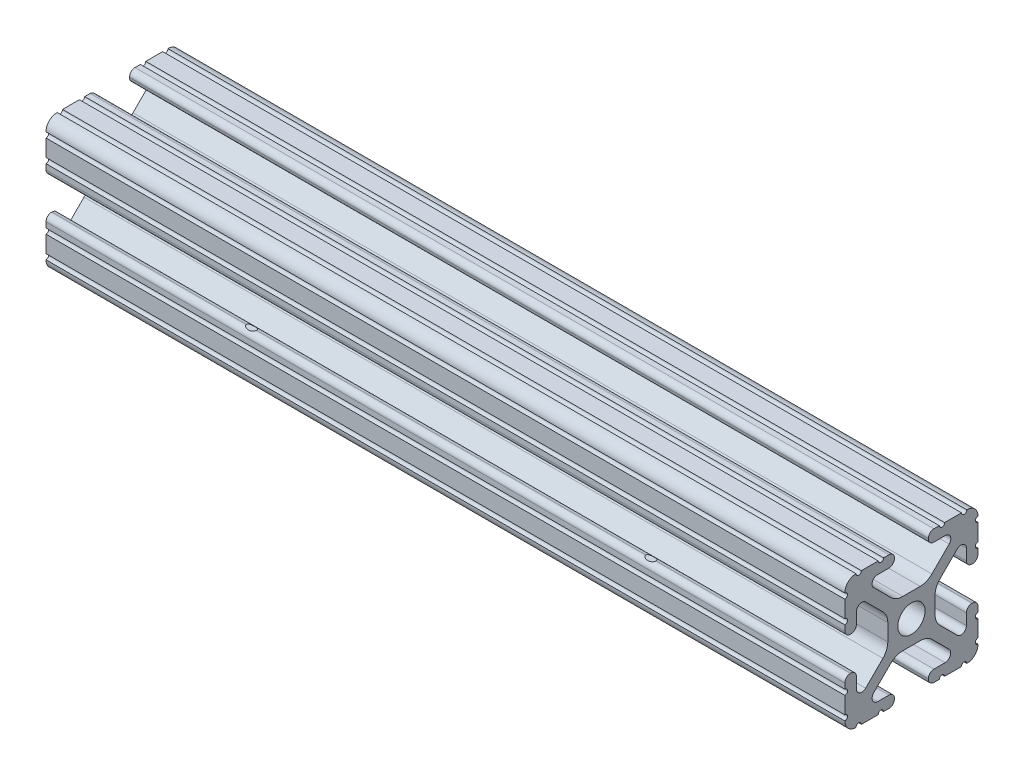
SolidWorks part; units mm, degrees
material "6061-T6 (SS)"
ref_plane "Front Plane" through (0, 0, 0) normal (0, 0, 1) x (1, 0, 0)
ref_plane "Top Plane" through (0, 0, 0) normal (0, 1, 0) x (1, 0, 0)
ref_plane "Right Plane" through (0, 0, 0) normal (1, 0, 0) x (0, 0, -1)
sketch "Sketch1" plane through (0, 0, 0) normal (1, 0, 0) x (0, 0, -1)
  line L0 (6.3331, -12.7) -> (9.5504, -12.7)
  line L1 (12.7, -9.5504) -> (12.7, -6.3331)
  line L2 (12.7, -5.3171) -> (12.7, -4.2875)
  line L3 (11.651, -3.2385) -> (11.5392, -3.2385)
  line L4 (10.4902, -4.2875) -> (10.4902, -6.4021)
  line L5 (8.7371, -7.1294) -> (5.441, -3.8408)
  line L6 (4.5085, -1.5932) -> (4.5085, 1.5932)
  line L7 (5.441, 3.8408) -> (8.7371, 7.1294)
  line L8 (10.4902, 6.4021) -> (10.4902, 4.2875)
  line L9 (11.5392, 3.2385) -> (11.651, 3.2385)
  line L10 (12.7, 4.2875) -> (12.7, 5.3171)
  line L11 (12.7, 6.3331) -> (12.7, 9.5504)
  line L12 (9.5504, 12.7) -> (6.3331, 12.7)
  line L13 (5.3171, 12.7) -> (4.2875, 12.7)
  line L14 (3.2385, 11.651) -> (3.2385, 11.5392)
  line L15 (4.2875, 10.4902) -> (6.4768, 10.4902)
  line L16 (7.207, 8.7244) -> (3.8983, 5.4232)
  line L17 (1.6558, 4.4958) -> (-1.6558, 4.4958)
  line L18 (-3.8983, 5.4232) -> (-7.207, 8.7244)
  line L19 (-6.4768, 10.4902) -> (-4.2875, 10.4902)
  line L20 (-3.2385, 11.5392) -> (-3.2385, 11.651)
  line L21 (-4.2875, 12.7) -> (-5.3171, 12.7)
  line L22 (-6.3331, 12.7) -> (-9.5504, 12.7)
  line L23 (-12.7, 9.5504) -> (-12.7, 6.3331)
  line L24 (-12.7, 5.3171) -> (-12.7, 4.2875)
  line L25 (-11.651, 3.2385) -> (-11.5392, 3.2385)
  line L26 (-10.4902, 4.2875) -> (-10.4902, 6.4021)
  line L27 (-8.7371, 7.1294) -> (-5.441, 3.8408)
  line L28 (-4.5085, 1.5932) -> (-4.5085, -1.5932)
  line L29 (-5.441, -3.8408) -> (-8.7371, -7.1294)
  line L30 (-10.4902, -6.4021) -> (-10.4902, -4.2875)
  line L31 (-11.5392, -3.2385) -> (-11.651, -3.2385)
  line L32 (-12.7, -4.2875) -> (-12.7, -5.3171)
  line L33 (-12.7, -6.3331) -> (-12.7, -9.5504)
  line L34 (-9.5504, -12.7) -> (-6.3331, -12.7)
  line L35 (-5.3171, -12.7) -> (-4.2875, -12.7)
  line L36 (-3.2385, -11.651) -> (-3.2385, -11.5392)
  line L37 (-4.2875, -10.4902) -> (-6.4164, -10.4902)
  line L38 (-7.1797, -8.6452) -> (-3.9523, -5.4237)
  line L39 (-1.7093, -4.4958) -> (1.7093, -4.4958)
  line L40 (3.9523, -5.4237) -> (7.1797, -8.6452)
  line L41 (6.4164, -10.4902) -> (4.2875, -10.4902)
  line L42 (3.2385, -11.5392) -> (3.2385, -11.651)
  line L43 (4.2875, -12.7) -> (5.3171, -12.7)
  circle A0 centre (0, 0) radius 2.6035
  arc A1 (6.3331, -12.7) -> (5.3171, -12.7) centre (5.8251, -12.7) ccw
  arc A2 (10.5664, -12.6998) -> (9.5504, -12.7) centre (10.0584, -12.7) ccw
  arc A3 (10.5664, -12.6998) -> (12.6998, -10.5664) centre (10.5918, -10.5918) ccw
  arc A4 (12.7, -9.5504) -> (12.6998, -10.5664) centre (12.7, -10.0584) ccw
  arc A5 (12.7, -5.3171) -> (12.7, -6.3331) centre (12.7, -5.8251) ccw
  arc A6 (12.7, -4.2875) -> (11.651, -3.2385) centre (11.651, -4.2875) ccw
  arc A7 (11.5392, -3.2385) -> (10.4902, -4.2875) centre (11.5392, -4.2875) ccw
  arc A8 (8.7371, -7.1294) -> (10.4902, -6.4021) centre (9.4628, -6.4021) ccw
  arc A9 (5.441, 3.8408) -> (4.5085, 1.5932) centre (7.6835, 1.5932) ccw
  arc A10 (10.4902, 6.4021) -> (8.7371, 7.1294) centre (9.4628, 6.4021) ccw
  arc A11 (10.4902, 4.2875) -> (11.5392, 3.2385) centre (11.5392, 4.2875) ccw
  arc A12 (11.651, 3.2385) -> (12.7, 4.2875) centre (11.651, 4.2875) ccw
  arc A13 (12.7, 6.3331) -> (12.7, 5.3171) centre (12.7, 5.8251) ccw
  arc A14 (12.6998, 10.5664) -> (12.7, 9.5504) centre (12.7, 10.0584) ccw
  arc A15 (12.6998, 10.5664) -> (10.5664, 12.6998) centre (10.5918, 10.5918) ccw
  arc A16 (9.5504, 12.7) -> (10.5664, 12.6998) centre (10.0584, 12.7) ccw
  arc A17 (5.3171, 12.7) -> (6.3331, 12.7) centre (5.8251, 12.7) ccw
  arc A18 (4.2875, 12.7) -> (3.2385, 11.651) centre (4.2875, 11.651) ccw
  arc A19 (3.2385, 11.5392) -> (4.2875, 10.4902) centre (4.2875, 11.5392) ccw
  arc A20 (7.207, 8.7244) -> (6.4768, 10.4902) centre (6.4768, 9.4563) ccw
  arc A21 (1.6558, 4.4958) -> (3.8983, 5.4232) centre (1.6558, 7.6708) ccw
  arc A22 (-3.8983, 5.4232) -> (-1.6558, 4.4958) centre (-1.6558, 7.6708) ccw
  arc A23 (-6.4768, 10.4902) -> (-7.207, 8.7244) centre (-6.4768, 9.4563) ccw
  arc A24 (-4.2875, 10.4902) -> (-3.2385, 11.5392) centre (-4.2875, 11.5392) ccw
  arc A25 (-3.2385, 11.651) -> (-4.2875, 12.7) centre (-4.2875, 11.651) ccw
  arc A26 (-6.3331, 12.7) -> (-5.3171, 12.7) centre (-5.8251, 12.7) ccw
  arc A27 (-10.5664, 12.6998) -> (-9.5504, 12.7) centre (-10.0584, 12.7) ccw
  arc A28 (-10.5664, 12.6998) -> (-12.6998, 10.5664) centre (-10.5918, 10.5918) ccw
  arc A29 (-12.7, 9.5504) -> (-12.6998, 10.5664) centre (-12.7, 10.0584) ccw
  arc A30 (-12.7, 5.3171) -> (-12.7, 6.3331) centre (-12.7, 5.8251) ccw
  arc A31 (-12.7, 4.2875) -> (-11.651, 3.2385) centre (-11.651, 4.2875) ccw
  arc A32 (-11.5392, 3.2385) -> (-10.4902, 4.2875) centre (-11.5392, 4.2875) ccw
  arc A33 (-8.7371, 7.1294) -> (-10.4902, 6.4021) centre (-9.4628, 6.4021) ccw
  arc A34 (-4.5085, 1.5932) -> (-5.441, 3.8408) centre (-7.6835, 1.5932) ccw
  arc A35 (-5.441, -3.8408) -> (-4.5085, -1.5932) centre (-7.6835, -1.5932) ccw
  arc A36 (-10.4902, -6.4021) -> (-8.7371, -7.1294) centre (-9.4628, -6.4021) ccw
  arc A37 (-10.4902, -4.2875) -> (-11.5392, -3.2385) centre (-11.5392, -4.2875) ccw
  arc A38 (-11.651, -3.2385) -> (-12.7, -4.2875) centre (-11.651, -4.2875) ccw
  arc A39 (-12.7, -6.3331) -> (-12.7, -5.3171) centre (-12.7, -5.8251) ccw
  arc A40 (-12.6998, -10.5664) -> (-12.7, -9.5504) centre (-12.7, -10.0584) ccw
  arc A41 (-12.6998, -10.5664) -> (-10.5664, -12.6998) centre (-10.5918, -10.5918) ccw
  arc A42 (-9.5504, -12.7) -> (-10.5664, -12.6998) centre (-10.0584, -12.7) ccw
  arc A43 (-5.3171, -12.7) -> (-6.3331, -12.7) centre (-5.8251, -12.7) ccw
  arc A44 (-4.2875, -12.7) -> (-3.2385, -11.651) centre (-4.2875, -11.651) ccw
  arc A45 (-3.2385, -11.5392) -> (-4.2875, -10.4902) centre (-4.2875, -11.5392) ccw
  arc A46 (-7.1797, -8.6452) -> (-6.4164, -10.4902) centre (-6.4164, -9.4098) ccw
  arc A47 (-1.7093, -4.4958) -> (-3.9523, -5.4237) centre (-1.7093, -7.6708) ccw
  arc A48 (3.9523, -5.4237) -> (1.7093, -4.4958) centre (1.7093, -7.6708) ccw
  arc A49 (6.4164, -10.4902) -> (7.1797, -8.6452) centre (6.4164, -9.4098) ccw
  arc A50 (4.2875, -10.4902) -> (3.2385, -11.5392) centre (4.2875, -11.5392) ccw
  arc A51 (3.2385, -11.651) -> (4.2875, -12.7) centre (4.2875, -11.651) ccw
  arc A52 (5.441, -3.8408) -> (4.5085, -1.5932) centre (7.6835, -1.5932) cw
extrude "Boss-Extrude1" add sketch "Sketch1" along normal blind 152.4
sketch "Sketch2" plane through (0, 0, 0) normal (0, 0, 1) x (1, 0, 0)
  line L0 (152.4, -6.3331) -> (152.4, -9.5504) construction
  circle A0 centre (114.3, 0) radius 3.3782
  circle A1 centre (38.1, 0) radius 3.3782
  point P4 (0, 0)
  dimension "D1" = 6.7564
  dimension "D2" = 114.3
  dimension "D3" = 38.1
extrude "Cut-Extrude1" cut sketch "Sketch2" against normal through all both and the other way through all
